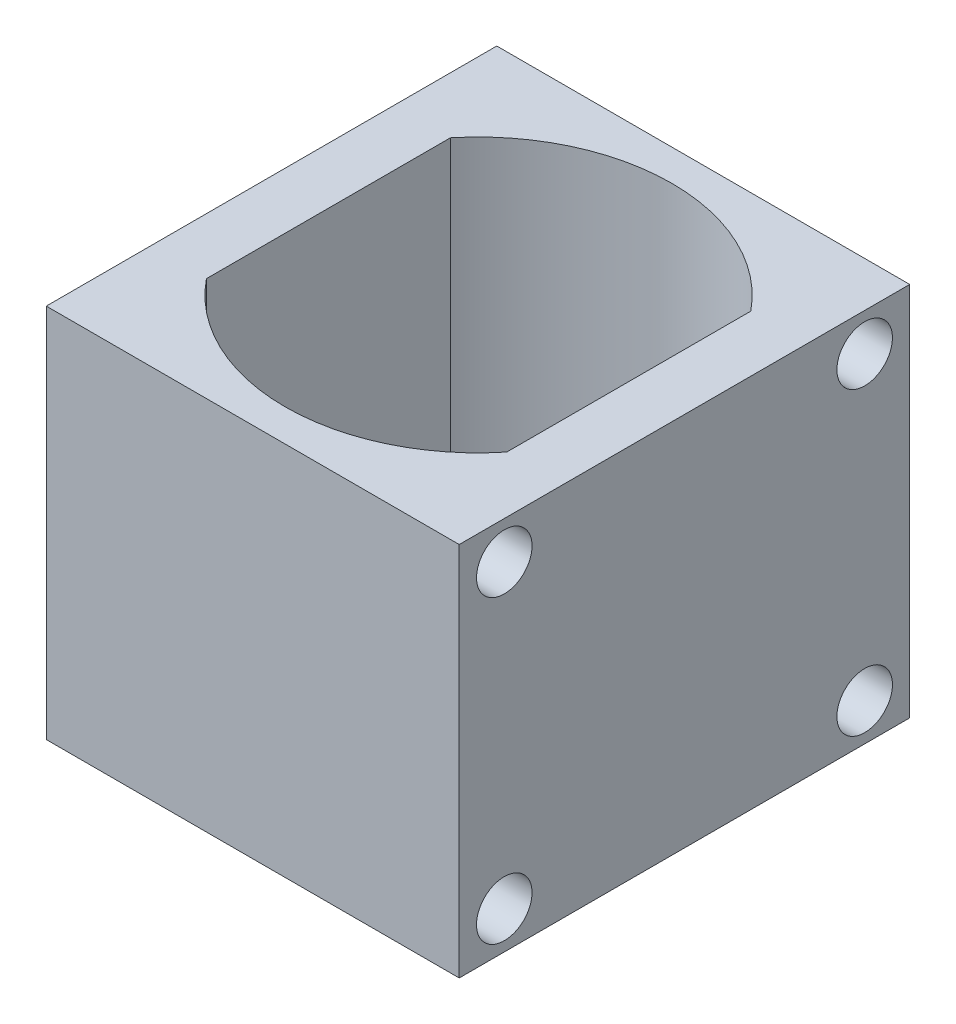
SolidWorks part; units mm, degrees
ref_plane "Front Plane" through (0, 0, 0) normal (0, 0, 1) x (1, 0, 0)
ref_plane "Top Plane" through (0, 0, 0) normal (0, 1, 0) x (1, 0, 0)
ref_plane "Right Plane" through (0, 0, 0) normal (1, 0, 0) x (0, 0, -1)
sketch "Sketch1" plane through (0, 0, 0) normal (0, 1, 0) x (1, 0, 0)
  line L0 (0, 12) -> (0, -12) construction
  line L1 (-11, 0) -> (-11, 12)
  line L2 (-11, 12) -> (11, 12)
  line L3 (11, 12) -> (11, -12)
  line L4 (11, -12) -> (-11, -12)
  line L5 (-11, -12) -> (-11, 0)
  line L6 (-8, 6.5325) -> (-8, -6.4675)
  line L7 (0, 0) -> (-8, 0) construction
  line L8 (8, 6.5325) -> (8, -6.4675)
  arc A1 (-8, 6.5325) -> (8, 6.5325) centre (0, 0) cw
  arc A2 (-8, -6.4675) -> (8, -6.4675) centre (0, 0) ccw
  dimension "D1" = 12
  dimension "D2" = 24
  dimension "D3" = 22
  dimension "D4" = 11
extrude "Boss-Extrude1" add sketch "Sketch1" along normal blind 20
sketch "Sketch2" plane through (11, 0, 0) normal (1, 0, 0) x (0, 0, -1)
  line L0 (-12, 20) -> (12, 0) construction
  line L1 (12, 20) -> (-12, 0) construction
  line L2 (0, 10) -> (0, 18) construction
  line L3 (0, 18) -> (-9.6, 18) construction
  line L4 (-12, 10) -> (12, 10) construction
  line L5 (-12, 20) -> (-12, 0) construction
  line L6 (12, 20) -> (12, 0) construction
  line L8 (-12, 20) -> (12, 20) construction
  circle A0 centre (-9.6, 18) radius 1.48
  circle A1 centre (9.6, 18) radius 1.48
  circle A2 centre (9.6, 2) radius 1.48
  circle A3 centre (-9.6, 2) radius 1.48
  dimension "D1" = 2.96
  dimension "D2" = 2.4
extrude "Cut-Extrude1" cut sketch "Sketch2" against normal blind 3
